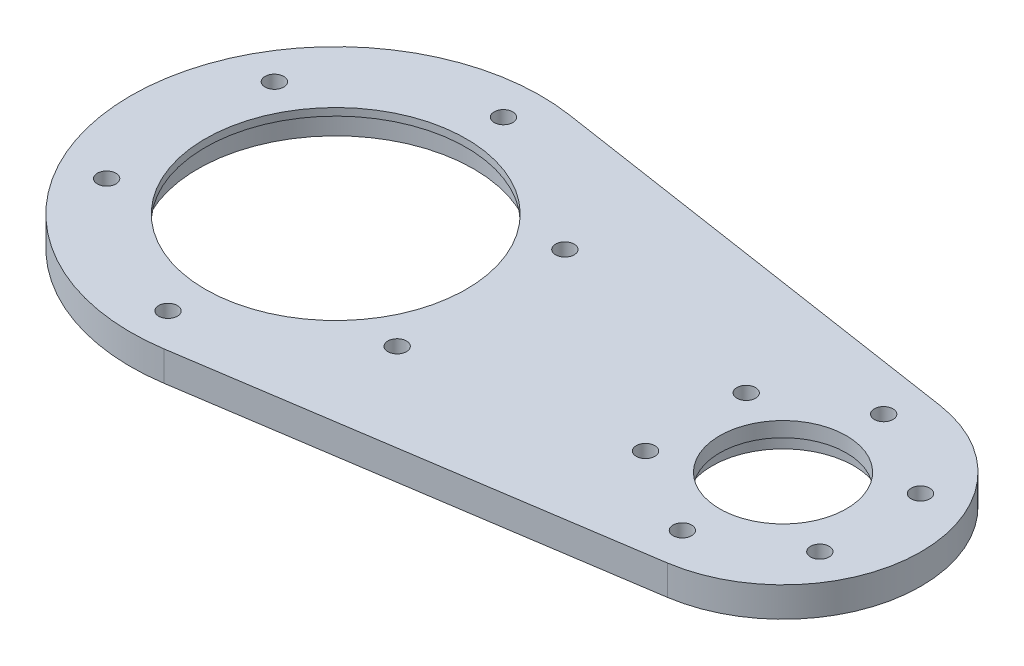
SolidWorks part; units mm, degrees
other "마크업1"
sketch "스케치8" plane through (80, 10, 22.5) normal (0.0741, 0.9433, 0.3234) x (0.9972, -0.0727, -0.0163)
sketch "스케치15" plane through (100, 13, 22.5) normal (0.0741, 0.9433, 0.3234) x (0.9972, -0.0727, -0.0163)
sketch "스케치16" plane through (100, 13, 22.5) normal (0.0741, 0.9433, 0.3234) x (0.9972, -0.0727, -0.0163)
sketch "스케치17" plane through (75, 13, 22.5) normal (0.0741, 0.9433, 0.3234) x (0.9972, -0.0727, -0.0163)
sketch "스케치23" plane through (75, 13, 22.5) normal (0.0741, 0.9433, 0.3234) x (0.9972, -0.0727, -0.0163)
sketch "스케치24" plane through (75, 10, 22.5) normal (0.0741, 0.9433, 0.3234) x (0.9972, -0.0727, -0.0163)
sketch "스케치25" plane through (75, 10, 25) normal (0.0741, 0.9433, 0.3234) x (0.9972, -0.0727, -0.0163)
sketch "스케치27" plane through (75, 10, 25) normal (0.0741, 0.9433, 0.3234) x (0.9972, -0.0727, -0.0163)
sketch "스케치29" plane through (75, 10, 25) normal (0.0741, 0.9433, 0.3234) x (0.9972, -0.0727, -0.0163)
sketch "스케치30" plane through (75, 10, 25) normal (0.0741, 0.9433, 0.3234) x (0.9972, -0.0727, -0.0163)
material "7075-T6 (SN)"
ref_plane "정면" through (0, 0, 0) normal (0, 0, 1) x (1, 0, 0)
ref_plane "윗면" through (0, 0, 0) normal (0, 1, 0) x (1, 0, 0)
ref_plane "우측면" through (0, 0, 0) normal (1, 0, 0) x (0, 0, -1)
sketch "스케치1" plane through (0, 0, 0) normal (0, 1, 0) x (1, 0, 0)
  circle A0 centre (0, 0) radius 17.5
  circle A1 centre (0, 0) radius 27.5
  dimension "D1" = 35
  dimension "D2" = 55
extrude "보스-돌출1" add sketch "스케치1" along normal blind 5 contours A1 | A0
sketch "스케치2" plane through (0, 5, 0) normal (0, 1, 0) x (1, 0, 0)
  circle A0 centre (0, 0) radius 18.5
  circle A1 centre (0, 0) radius 27.5 construction
  circle A2 centre (0, 0) radius 27.5
  dimension "D1" = 37
extrude "보스-돌출2" add sketch "스케치2" along normal blind 5
sketch "스케치3" plane through (0, 10, 0) normal (0, 1, 0) x (1, 0, 0)
  line L0 (4.125, 27.1889) -> (62.775, 18.2907)
  line L1 (0, 0) -> (60, 0) construction
  line L2 (4.125, -27.1889) -> (62.775, -18.2907)
  circle A0 centre (0, 0) radius 27.5 construction
  arc A1 (4.125, -27.1889) -> (4.125, 27.1889) centre (0, 0) ccw
  arc A2 (62.775, -18.2907) -> (62.775, 18.2907) centre (60, 0) ccw
  dimension "D2" = 37
  dimension "D1" = 60
extrude "보스-돌출3" add sketch "스케치3" against normal blind 9
sketch "스케치7" plane through (0, 5, 0) normal (0, 1, 0) x (1, 0, 0)
  circle A0 centre (0, 0) radius 18.5 construction
  circle A1 centre (0, 0) radius 18.5
extrude "컷-돌출4" cut sketch "스케치7" against normal blind 4
sketch "스케치13" plane through (0, 1, 0) normal (0, -1, 0) x (1, 0, 0)
  circle A0 centre (60, 0) radius 9.5
  dimension "D1" = 19
extrude "컷-돌출9" cut sketch "스케치13" against normal blind 7
sketch "스케치14" plane through (0, 8, 0) normal (0, -1, 0) x (1, 0, 0)
  circle A0 centre (60, 0) radius 8.5
  dimension "D1" = 17
extrude "컷-돌출10" cut sketch "스케치14" against normal through all
sketch "스케치26" plane through (0, 0, 0) normal (1, 0, 0) x (0, 0, -1)
  line L1 (-33.8225, -8.2842) -> (31.4643, -8.2842)
  line L2 (-33.8225, -8.2842) -> (-33.8225, 6)
  line L3 (-33.8225, 6) -> (31.4643, 6)
  line L4 (31.4643, -8.2842) -> (31.4643, 6)
  line L5 (-27.5, 0) -> (27.5, 0) construction
  dimension "D1" = 6
extrude "컷-돌출11" cut sketch "스케치26" against normal mid plane 2222
sketch "스케치28" plane through (0, 10, 0) normal (0, 1, 0) x (1, 0, 0)
  circle A0 centre (0, 0) radius 18.5
  circle A1 centre (0, 0) radius 18.5 construction
  circle A2 centre (0, 0) radius 17.5
  dimension "D1" = 35
extrude "보스-돌출4" add sketch "스케치28" against normal blind 1
sketch "스케치31" plane through (0, 6, 0) normal (0, -1, 0) x (1, 0, 0)
  circle A0 centre (0, 0) radius 22.5 construction
  circle A1 centre (0, 0) radius 18.5 construction
  dimension "D1" = 45
hole_wizard "M3 탭을 위한 탭 드릴1" positions "스케치32" profile "스케치33" hole size "M3" standard "ISO" end condition through all
sketch "스케치32" plane through (0, 6, 0) normal (0, -1, 0) x (-1, 0, 0)
  circle A0 centre (0, 0) radius 22.5 construction
  point P0 (0, 22.5)
sketch "스케치33" plane through (0, 6, -22.5) normal (1, 0, 0) x (0, 0, -1)
  line L0 (0, 0) -> (0, 4)
  line L1 (0, 4) -> (1.25, 4)
  line L2 (1.25, 4) -> (1.25, 0)
  line L5 (1.25, 0) -> (0, 0)
  line L11 (0, -6.35) -> (0, 107.95) construction
  dimension "관통 구멍 지름" = 2.5
  dimension "관통 구멍 깊이" = 4
pattern_circular "원형 패턴1" count 6 over 360 about axis through (0, 0, 0) along (0, 1, 0) of "M3 탭을 위한 탭 드릴1"
sketch "스케치34" plane through (0, 6, 0) normal (0, -1, 0) x (1, 0, 0)
  circle A0 centre (60, 0) radius 13.5 construction
  circle A1 centre (60, 0) radius 8.5 construction
  dimension "D1" = 27
hole_wizard "M3 탭을 위한 탭 드릴2" positions "스케치35" profile "스케치36" hole size "M3" standard "ISO" end condition through all
sketch "스케치35" plane through (0, 6, 0) normal (0, -1, 0) x (-1, 0, 0)
  circle A0 centre (-60, 0) radius 13.5 construction
  point P0 (-60, 13.5)
sketch "스케치36" plane through (60, 6, -13.5) normal (1, 0, 0) x (0, 0, -1)
  line L0 (0, 0) -> (0, 4)
  line L1 (0, 4) -> (1.25, 4)
  line L2 (1.25, 4) -> (1.25, 0)
  line L5 (1.25, 0) -> (0, 0)
  line L11 (0, -6.35) -> (0, 107.95) construction
  dimension "관통 구멍 지름" = 2.5
  dimension "관통 구멍 깊이" = 4
pattern_circular "원형 패턴2" count 6 over 360 about axis through (60, 0, 0) along (0, 1, 0) of "M3 탭을 위한 탭 드릴2"
